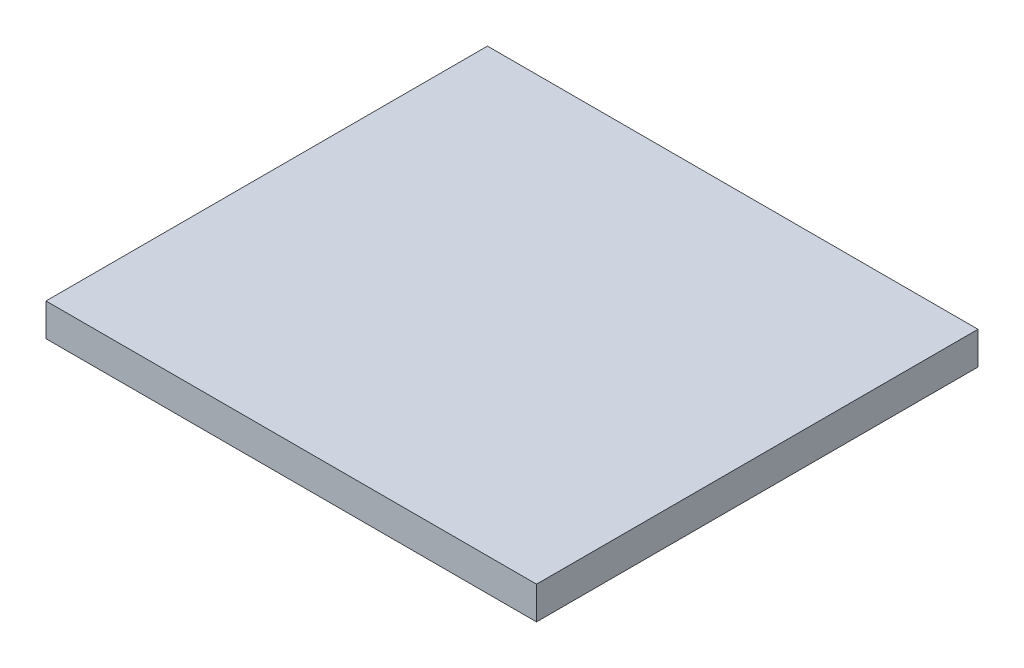
SolidWorks part; units mm, degrees
ref_plane "Front Plane" through (0, 0, 0) normal (0, 0, 1) x (1, 0, 0)
ref_plane "Top Plane" through (0, 0, 0) normal (0, 1, 0) x (1, 0, 0)
ref_plane "Right Plane" through (0, 0, 0) normal (1, 0, 0) x (0, 0, -1)
sketch "Sketch1" plane through (0, 0, 0) normal (0, 0, 1) x (1, 0, 0)
  line L9 (-75, 5) -> (75, 5)
  line L10 (-75, 5) -> (-75, -5)
  line L11 (-75, -5) -> (75, -5)
  line L12 (75, 5) -> (75, -5)
  line L13 (-75, 5) -> (75, -5) construction
  line L14 (-75, -5) -> (75, 5) construction
  point P0 (0, 0)
  dimension "D1" = 10
  dimension "D2" = 150
extrude "Boss-Extrude1" add sketch "Sketch1" along normal blind 135
